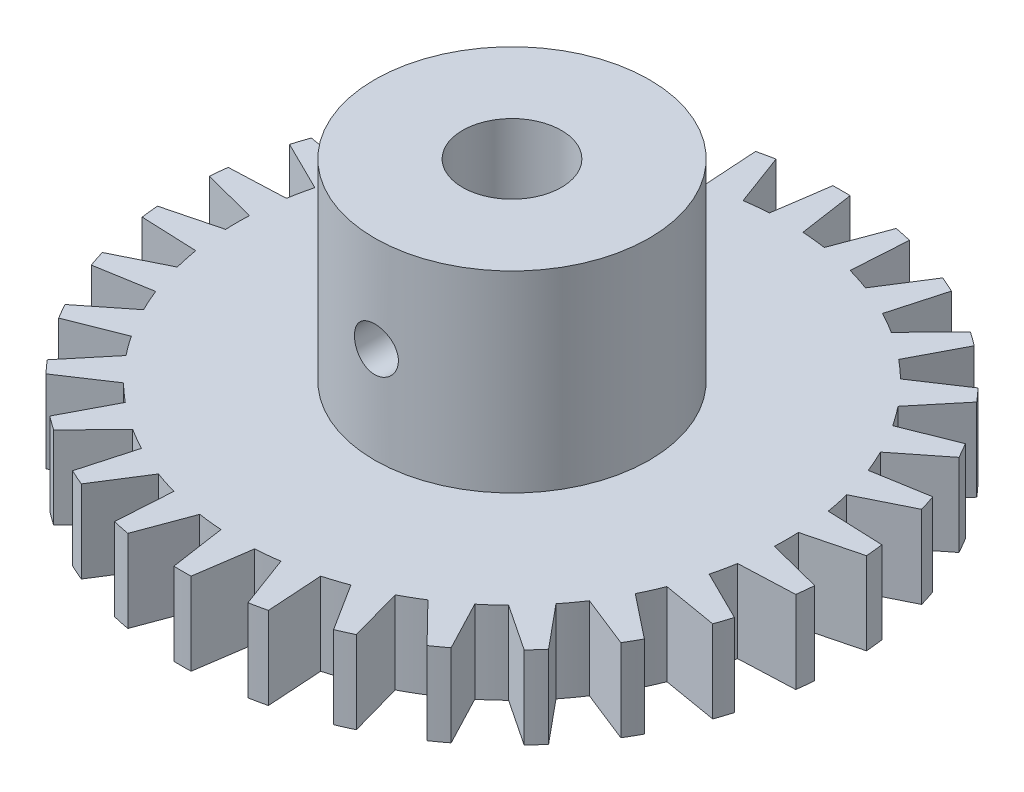
SolidWorks part; units mm, degrees
ref_plane "Front Plane" through (0, 0, 0) normal (0, 0, 1) x (1, 0, 0)
ref_plane "Top Plane" through (0, 0, 0) normal (0, 1, 0) x (1, 0, 0)
ref_plane "Right Plane" through (0, 0, 0) normal (1, 0, 0) x (0, 0, -1)
sketch "Sketch1" plane through (0, 0, 0) normal (0, 1, 0) x (1, 0, 0)
  line L0 (0, 0) -> (0, 12) construction
  line L1 (0, 0) -> (-0.3141, 11.9959) construction
  line L2 (0, 0) -> (-0.6105, 9.9813) construction
  line L3 (0, 0) -> (-1.0453, 9.9452) construction
  line L4 (-0.3141, 11.9959) -> (-0.6105, 9.9813)
  line L5 (0.3141, 11.9959) -> (0.6105, 9.9813)
  line L6 (2.1868, 11.7991) -> (1.4781, 9.8902)
  line L7 (2.8013, 11.6684) -> (2.6724, 9.6363)
  line L8 (4.5922, 11.0866) -> (3.5021, 9.3667)
  line L9 (5.1661, 10.831) -> (4.6175, 8.8701)
  line L10 (6.7969, 9.8895) -> (5.373, 8.4339)
  line L11 (7.3051, 9.5202) -> (6.3608, 7.7162)
  line L12 (8.7045, 8.2603) -> (7.0091, 7.1325)
  line L13 (9.1249, 7.7934) -> (7.8261, 6.2251)
  line L14 (10.2317, 6.27) -> (8.3389, 5.5194)
  line L15 (10.5458, 5.7259) -> (8.9493, 4.462)
  line L16 (11.3117, 4.0057) -> (9.3042, 3.665)
  line L17 (11.5058, 3.4082) -> (9.6815, 2.5038)
  line L18 (11.8973, 1.5663) -> (9.8629, 1.6505)
  line L19 (11.963, 0.9415) -> (9.9905, 0.4362)
  line L20 (11.963, -0.9415) -> (9.9905, -0.4362)
  line L21 (11.8973, -1.5663) -> (9.8629, -1.6505)
  line L22 (11.5058, -3.4082) -> (9.6815, -2.5038)
  line L23 (11.3117, -4.0057) -> (9.3042, -3.665)
  line L24 (10.5458, -5.7259) -> (8.9493, -4.462)
  line L25 (10.2317, -6.27) -> (8.3389, -5.5194)
  line L26 (9.1249, -7.7934) -> (7.8261, -6.2251)
  line L27 (8.7045, -8.2603) -> (7.0091, -7.1325)
  line L28 (7.3051, -9.5202) -> (6.3608, -7.7162)
  line L29 (6.7969, -9.8895) -> (5.373, -8.4339)
  line L30 (5.1661, -10.831) -> (4.6175, -8.8701)
  line L31 (4.5922, -11.0866) -> (3.5021, -9.3667)
  line L32 (2.8013, -11.6684) -> (2.6724, -9.6363)
  line L33 (2.1868, -11.7991) -> (1.4781, -9.8902)
  line L34 (0.3141, -11.9959) -> (0.6105, -9.9813)
  line L35 (-0.3141, -11.9959) -> (-0.6105, -9.9813)
  line L36 (-2.1868, -11.7991) -> (-1.4781, -9.8902)
  line L37 (-2.8013, -11.6684) -> (-2.6724, -9.6363)
  line L38 (-4.5922, -11.0866) -> (-3.5021, -9.3667)
  line L39 (-5.1661, -10.831) -> (-4.6175, -8.8701)
  line L40 (-6.7969, -9.8895) -> (-5.373, -8.4339)
  line L41 (-7.3051, -9.5202) -> (-6.3608, -7.7162)
  line L42 (-8.7045, -8.2603) -> (-7.0091, -7.1325)
  line L43 (-9.1249, -7.7934) -> (-7.8261, -6.2251)
  line L44 (-10.2317, -6.27) -> (-8.3389, -5.5194)
  line L45 (-10.5458, -5.7259) -> (-8.9493, -4.462)
  line L46 (-11.3117, -4.0057) -> (-9.3042, -3.665)
  line L47 (-11.5058, -3.4082) -> (-9.6815, -2.5038)
  line L48 (-11.8973, -1.5663) -> (-9.8629, -1.6505)
  line L49 (-11.963, -0.9415) -> (-9.9905, -0.4362)
  line L50 (-11.963, 0.9415) -> (-9.9905, 0.4362)
  line L51 (-11.8973, 1.5663) -> (-9.8629, 1.6505)
  line L52 (-11.5058, 3.4082) -> (-9.6815, 2.5038)
  line L53 (-11.3117, 4.0057) -> (-9.3042, 3.665)
  line L54 (-10.5458, 5.7259) -> (-8.9493, 4.462)
  line L55 (-10.2317, 6.27) -> (-8.3389, 5.5194)
  line L56 (-9.1249, 7.7934) -> (-7.8261, 6.2251)
  line L57 (-8.7045, 8.2603) -> (-7.0091, 7.1325)
  line L58 (-7.3051, 9.5202) -> (-6.3608, 7.7162)
  line L59 (-6.7969, 9.8895) -> (-5.373, 8.4339)
  line L60 (-5.1661, 10.831) -> (-4.6175, 8.8701)
  line L61 (-4.5922, 11.0866) -> (-3.5021, 9.3667)
  line L62 (-2.8013, 11.6684) -> (-2.6724, 9.6363)
  line L63 (-2.1868, 11.7991) -> (-1.4781, 9.8902)
  arc A0 (0.3141, 11.9959) -> (-0.3141, 11.9959) centre (0, 0) ccw
  arc A1 (-0.6105, 9.9813) -> (-1.0453, 9.9452) centre (0, 0) ccw
  arc A2 (0.6105, 9.9813) -> (1.0453, 9.9452) centre (0, 0) cw
  arc A4 (2.8013, 11.6684) -> (2.1868, 11.7991) centre (0, 0) ccw
  arc A5 (1.4781, 9.8902) -> (1.0453, 9.9452) centre (0, 0) ccw
  arc A6 (2.6724, 9.6363) -> (3.0902, 9.5106) centre (0, 0) cw
  arc A7 (5.1661, 10.831) -> (4.5922, 11.0866) centre (0, 0) ccw
  arc A8 (3.5021, 9.3667) -> (3.0902, 9.5106) centre (0, 0) ccw
  arc A9 (4.6175, 8.8701) -> (5, 8.6603) centre (0, 0) cw
  arc A10 (7.3051, 9.5202) -> (6.7969, 9.8895) centre (0, 0) ccw
  arc A11 (5.373, 8.4339) -> (5, 8.6603) centre (0, 0) ccw
  arc A12 (6.3608, 7.7162) -> (6.6913, 7.4314) centre (0, 0) cw
  arc A13 (9.1249, 7.7934) -> (8.7045, 8.2603) centre (0, 0) ccw
  arc A14 (7.0091, 7.1325) -> (6.6913, 7.4314) centre (0, 0) ccw
  arc A15 (7.8261, 6.2251) -> (8.0902, 5.8779) centre (0, 0) cw
  arc A16 (10.5458, 5.7259) -> (10.2317, 6.27) centre (0, 0) ccw
  arc A17 (8.3389, 5.5194) -> (8.0902, 5.8779) centre (0, 0) ccw
  arc A18 (8.9493, 4.462) -> (9.1355, 4.0674) centre (0, 0) cw
  arc A19 (11.5058, 3.4082) -> (11.3117, 4.0057) centre (0, 0) ccw
  arc A20 (9.3042, 3.665) -> (9.1355, 4.0674) centre (0, 0) ccw
  arc A21 (9.6815, 2.5038) -> (9.7815, 2.0791) centre (0, 0) cw
  arc A22 (11.963, 0.9415) -> (11.8973, 1.5663) centre (0, 0) ccw
  arc A23 (9.8629, 1.6505) -> (9.7815, 2.0791) centre (0, 0) ccw
  arc A24 (9.9905, 0.4362) -> (10, 0) centre (0, 0) cw
  arc A25 (11.8973, -1.5663) -> (11.963, -0.9415) centre (0, 0) ccw
  arc A26 (9.9905, -0.4362) -> (10, 0) centre (0, 0) ccw
  arc A27 (9.8629, -1.6505) -> (9.7815, -2.0791) centre (0, 0) cw
  arc A28 (11.3117, -4.0057) -> (11.5058, -3.4082) centre (0, 0) ccw
  arc A29 (9.6815, -2.5038) -> (9.7815, -2.0791) centre (0, 0) ccw
  arc A30 (9.3042, -3.665) -> (9.1355, -4.0674) centre (0, 0) cw
  arc A31 (10.2317, -6.27) -> (10.5458, -5.7259) centre (0, 0) ccw
  arc A32 (8.9493, -4.462) -> (9.1355, -4.0674) centre (0, 0) ccw
  arc A33 (8.3389, -5.5194) -> (8.0902, -5.8779) centre (0, 0) cw
  arc A34 (8.7045, -8.2603) -> (9.1249, -7.7934) centre (0, 0) ccw
  arc A35 (7.8261, -6.2251) -> (8.0902, -5.8779) centre (0, 0) ccw
  arc A36 (7.0091, -7.1325) -> (6.6913, -7.4314) centre (0, 0) cw
  arc A37 (6.7969, -9.8895) -> (7.3051, -9.5202) centre (0, 0) ccw
  arc A38 (6.3608, -7.7162) -> (6.6913, -7.4314) centre (0, 0) ccw
  arc A39 (5.373, -8.4339) -> (5, -8.6603) centre (0, 0) cw
  arc A40 (4.5922, -11.0866) -> (5.1661, -10.831) centre (0, 0) ccw
  arc A41 (4.6175, -8.8701) -> (5, -8.6603) centre (0, 0) ccw
  arc A42 (3.5021, -9.3667) -> (3.0902, -9.5106) centre (0, 0) cw
  arc A43 (2.1868, -11.7991) -> (2.8013, -11.6684) centre (0, 0) ccw
  arc A44 (2.6724, -9.6363) -> (3.0902, -9.5106) centre (0, 0) ccw
  arc A45 (1.4781, -9.8902) -> (1.0453, -9.9452) centre (0, 0) cw
  arc A46 (-0.3141, -11.9959) -> (0.3141, -11.9959) centre (0, 0) ccw
  arc A47 (0.6105, -9.9813) -> (1.0453, -9.9452) centre (0, 0) ccw
  arc A48 (-0.6105, -9.9813) -> (-1.0453, -9.9452) centre (0, 0) cw
  arc A49 (-2.8013, -11.6684) -> (-2.1868, -11.7991) centre (0, 0) ccw
  arc A50 (-1.4781, -9.8902) -> (-1.0453, -9.9452) centre (0, 0) ccw
  arc A51 (-2.6724, -9.6363) -> (-3.0902, -9.5106) centre (0, 0) cw
  arc A52 (-5.1661, -10.831) -> (-4.5922, -11.0866) centre (0, 0) ccw
  arc A53 (-3.5021, -9.3667) -> (-3.0902, -9.5106) centre (0, 0) ccw
  arc A54 (-4.6175, -8.8701) -> (-5, -8.6603) centre (0, 0) cw
  arc A55 (-7.3051, -9.5202) -> (-6.7969, -9.8895) centre (0, 0) ccw
  arc A56 (-5.373, -8.4339) -> (-5, -8.6603) centre (0, 0) ccw
  arc A57 (-6.3608, -7.7162) -> (-6.6913, -7.4314) centre (0, 0) cw
  arc A58 (-9.1249, -7.7934) -> (-8.7045, -8.2603) centre (0, 0) ccw
  arc A59 (-7.0091, -7.1325) -> (-6.6913, -7.4314) centre (0, 0) ccw
  arc A60 (-7.8261, -6.2251) -> (-8.0902, -5.8779) centre (0, 0) cw
  arc A61 (-10.5458, -5.7259) -> (-10.2317, -6.27) centre (0, 0) ccw
  arc A62 (-8.3389, -5.5194) -> (-8.0902, -5.8779) centre (0, 0) ccw
  arc A63 (-8.9493, -4.462) -> (-9.1355, -4.0674) centre (0, 0) cw
  arc A64 (-11.5058, -3.4082) -> (-11.3117, -4.0057) centre (0, 0) ccw
  arc A65 (-9.3042, -3.665) -> (-9.1355, -4.0674) centre (0, 0) ccw
  arc A66 (-9.6815, -2.5038) -> (-9.7815, -2.0791) centre (0, 0) cw
  arc A67 (-11.963, -0.9415) -> (-11.8973, -1.5663) centre (0, 0) ccw
  arc A68 (-9.8629, -1.6505) -> (-9.7815, -2.0791) centre (0, 0) ccw
  arc A69 (-9.9905, -0.4362) -> (-10, 0) centre (0, 0) cw
  arc A70 (-11.8973, 1.5663) -> (-11.963, 0.9415) centre (0, 0) ccw
  arc A71 (-9.9905, 0.4362) -> (-10, 0) centre (0, 0) ccw
  arc A72 (-9.8629, 1.6505) -> (-9.7815, 2.0791) centre (0, 0) cw
  arc A73 (-11.3117, 4.0057) -> (-11.5058, 3.4082) centre (0, 0) ccw
  arc A74 (-9.6815, 2.5038) -> (-9.7815, 2.0791) centre (0, 0) ccw
  arc A75 (-9.3042, 3.665) -> (-9.1355, 4.0674) centre (0, 0) cw
  arc A76 (-10.2317, 6.27) -> (-10.5458, 5.7259) centre (0, 0) ccw
  arc A77 (-8.9493, 4.462) -> (-9.1355, 4.0674) centre (0, 0) ccw
  arc A78 (-8.3389, 5.5194) -> (-8.0902, 5.8779) centre (0, 0) cw
  arc A79 (-8.7045, 8.2603) -> (-9.1249, 7.7934) centre (0, 0) ccw
  arc A80 (-7.8261, 6.2251) -> (-8.0902, 5.8779) centre (0, 0) ccw
  arc A81 (-7.0091, 7.1325) -> (-6.6913, 7.4314) centre (0, 0) cw
  arc A82 (-6.7969, 9.8895) -> (-7.3051, 9.5202) centre (0, 0) ccw
  arc A83 (-6.3608, 7.7162) -> (-6.6913, 7.4314) centre (0, 0) ccw
  arc A84 (-5.373, 8.4339) -> (-5, 8.6603) centre (0, 0) cw
  arc A85 (-4.5922, 11.0866) -> (-5.1661, 10.831) centre (0, 0) ccw
  arc A86 (-4.6175, 8.8701) -> (-5, 8.6603) centre (0, 0) ccw
  arc A87 (-3.5021, 9.3667) -> (-3.0902, 9.5106) centre (0, 0) cw
  arc A88 (-2.1868, 11.7991) -> (-2.8013, 11.6684) centre (0, 0) ccw
  arc A89 (-2.6724, 9.6363) -> (-3.0902, 9.5106) centre (0, 0) ccw
  arc A90 (-1.4781, 9.8902) -> (-1.0453, 9.9452) centre (0, 0) cw
  point P185 (0, 0)
  dimension "D1" = 1.5
  dimension "D2" = 2
  dimension "D3" = 2.5
  dimension "D4" = 30
  dimension "D5" = 10
extrude "Boss-Extrude1" add sketch "Sketch1" along normal blind 3
sketch "Sketch3" plane through (0, 3, 0) normal (0, 1, 0) x (1, 0, 0)
  circle A1 centre (0, 0) radius 5
  dimension "D2" = 10
extrude "Boss-Extrude2" add sketch "Sketch3" along normal blind 7
sketch "Sketch2" plane through (0, 3, 0) normal (0, 1, 0) x (1, 0, 0)
  circle A0 centre (0, 0) radius 1.8
  dimension "D1" = 3.6
extrude "Cut-Extrude1" cut sketch "Sketch2" against normal through all and the other way through all
sketch "Sketch4" plane through (0, 0, 0) normal (0, 0, 1) x (1, 0, 0)
  line L1 (5, 10) -> (-5, 10) construction
  circle A0 centre (0, 6.5) radius 0.8
  dimension "D1" = 1.6
  dimension "D2" = 3.5
extrude "Cut-Extrude2" cut sketch "Sketch4" along normal through all
